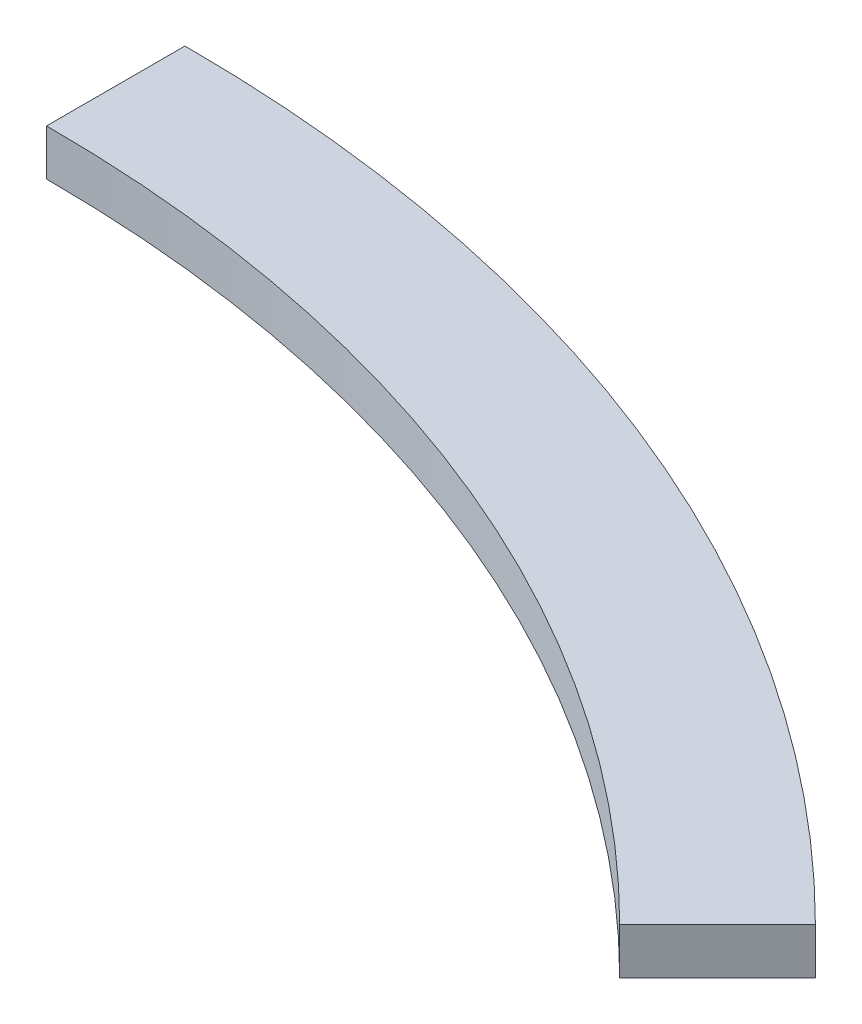
SolidWorks part; units mm, degrees
ref_plane "Front Plane" through (0, 0, 0) normal (0, 0, 1) x (1, 0, 0)
ref_plane "Top Plane" through (0, 0, 0) normal (0, 1, 0) x (1, 0, 0)
ref_plane "Right Plane" through (0, 0, 0) normal (1, 0, 0) x (0, 0, -1)
sketch "Sketch1" plane through (0, 0, 0) normal (0, 1, 0) x (1, 0, 0)
  line L0 (0, 0) -> (0, 300) construction
  line L1 (0, 300) -> (0, 330)
  line L2 (0, 0) -> (233.3452, 233.3452) construction
  line L3 (212.132, 212.132) -> (233.3452, 233.3452)
  arc A0 (0, 300) -> (212.132, 212.132) centre (0, 0) cw
  arc A1 (0, 330) -> (233.3452, 233.3452) centre (0, 0) cw
  dimension "D1" = 30
  dimension "D2" = 300
  dimension "D3" = 45
  dimension "D4" = 330
extrude "Boss-Extrude1" add sketch "Sketch1" along normal blind 10 contours A1 L1 A0 L3
